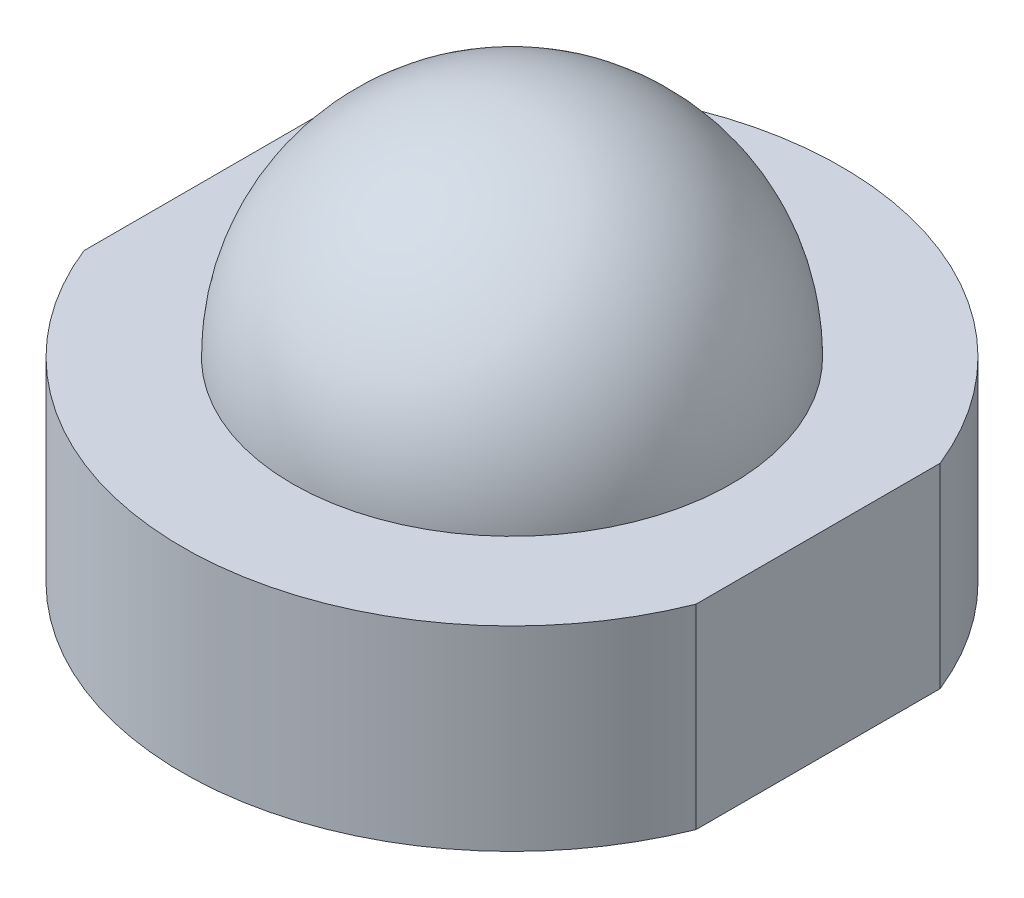
SolidWorks part; units mm, degrees
ref_plane "Front Plane" through (0, 0, 0) normal (0, 0, 1) x (1, 0, 0)
ref_plane "Top Plane" through (0, 0, 0) normal (0, 1, 0) x (1, 0, 0)
ref_plane "Right Plane" through (0, 0, 0) normal (1, 0, 0) x (0, 0, -1)
sketch "Sketch1" plane through (0, 0, 0) normal (0, 1, 0) x (1, 0, 0)
  line L0 (3.762, 1.5) -> (3.762, -1.5)
  line L1 (0, 0) -> (0, 50000) construction
  line L2 (-3.762, 1.5) -> (-3.762, -1.5)
  circle A0 centre (0, 0) radius 4.05
  dimension "D1" = 8.1
  dimension "D2" = 3
extrude "Boss-Extrude1" add sketch "Sketch1" along normal blind 2.4 contours A0 L1 L2 | L1 A0 L0
sketch "Sketch3" plane through (0, 0, 0) normal (1, 0, 0) x (0, 0, -1)
  line L1 (4.05, 2.4) -> (1.5, 2.4) construction
  line L2 (0, 2.4) -> (0, 5.1)
  line L3 (0, 2.4) -> (2.7, 2.4)
  arc A0 (2.7, 2.4) -> (0, 5.1) centre (0, 2.4) ccw
  dimension "D1" = 2.7
revolve "Revolve1" add sketch "Sketch3" angle 360 about L2
equation "\"D1@Sketch3\"=5.4/2"
